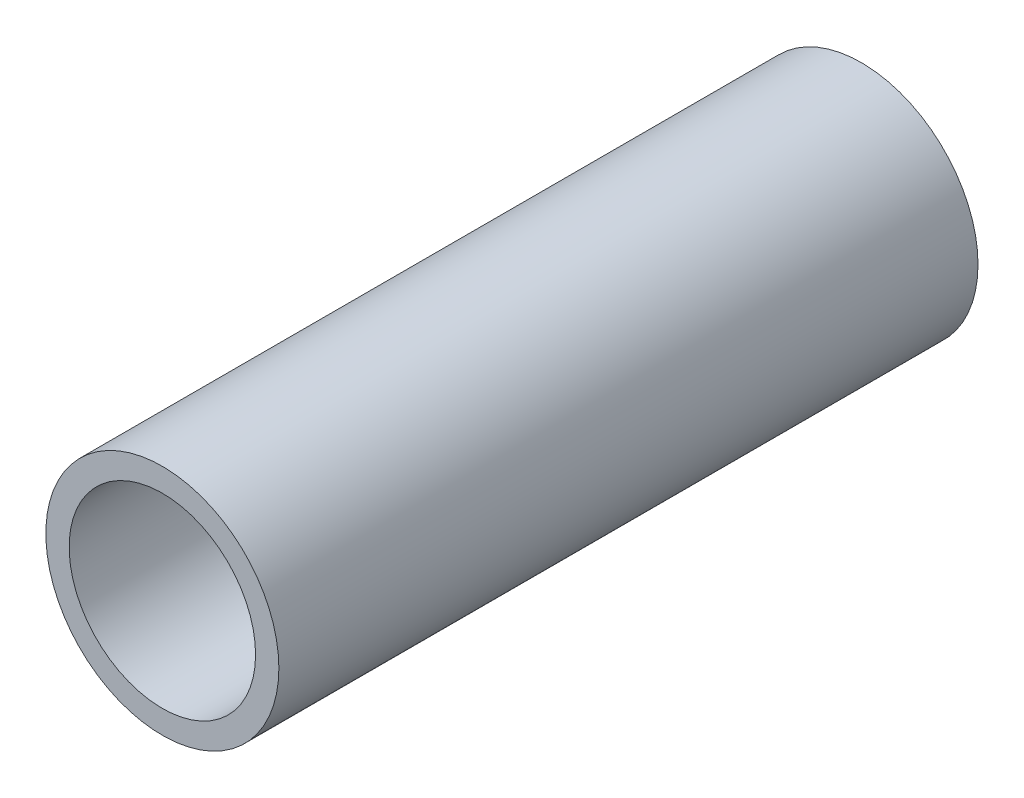
SolidWorks part; units mm, degrees
ref_plane "Front Plane" through (0, 0, 0) normal (0, 0, 1) x (1, 0, 0)
ref_plane "Top Plane" through (0, 0, 0) normal (0, 1, 0) x (1, 0, 0)
ref_plane "Right Plane" through (0, 0, 0) normal (1, 0, 0) x (0, 0, -1)
sketch "Sketch1" plane through (0, 0, 0) normal (0, 0, 1) x (1, 0, 0)
  circle A0 centre (0, 0) radius 1.25
  circle A1 centre (0, 0) radius 1
extrude "Boss-Extrude1" add sketch "Sketch1" along normal blind 7.5
